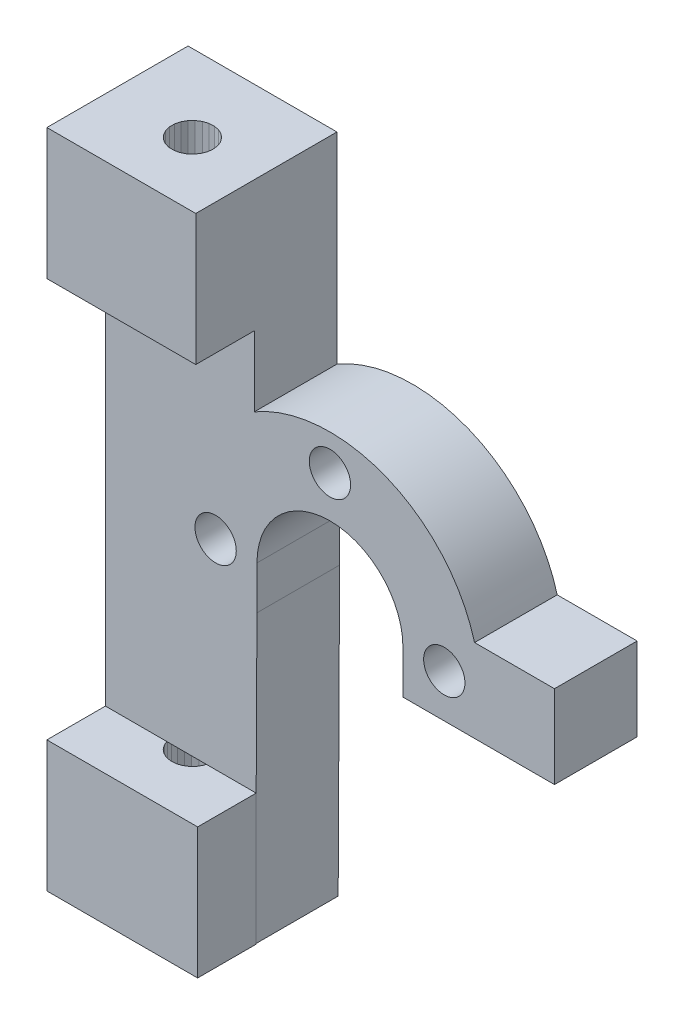
SolidWorks part; units mm, degrees
ref_plane "Front Plane" through (0, 0, 0) normal (0, 0, 1) x (1, 0, 0)
ref_plane "Top Plane" through (0, 0, 0) normal (0, 1, 0) x (1, 0, 0)
ref_plane "Right Plane" through (0, 0, 0) normal (1, 0, 0) x (0, 0, -1)
sketch "Sketch1" plane through (0, 0, 84.4516) normal (0, 0, 1) x (1, 0, 0)
  line L0 (24.9234, 11.702) -> (44.5234, 11.702) construction
  line L4 (45.6141, 11.702) -> (44.5234, 11.702) construction
  line L5 (40.0234, 11.702) -> (40.0234, 8.5665)
  line L6 (29.4234, 11.702) -> (29.4234, 8.5665)
  line L7 (40.0234, 8.5665) -> (47.0234, 8.5665)
  line L9 (45.6141, 11.702) -> (45.6141, 25.0304) construction
  line L11 (18.4234, 14.5957) -> (18.4234, 8.5665)
  line L14 (47.0234, 8.5665) -> (51.0234, 8.5665)
  line L15 (51.0234, 8.5665) -> (51.0234, 14.5957)
  line L16 (51.0234, 14.5957) -> (45.2226, 14.5957)
  line L18 (19.3206, -12.2967) -> (29.3206, -12.2967) construction
  line L20 (29.3206, 35.7033) -> (19.3206, 35.7033) construction
  line L21 (29.2311, 35.7033) -> (19.3206, 35.7033) construction
  line L22 (18.4234, 14.5957) -> (18.4234, 35.7033)
  line L23 (29.2311, 35.7033) -> (29.2311, 21.1063)
  line L25 (19.3206, -12.2967) -> (29.3206, -12.2967) construction
  line L26 (18.4234, 8.5665) -> (18.4234, -12.2967)
  line L27 (29.4234, 8.5665) -> (29.3206, -12.2967)
  line L28 (29.3206, -12.2967) -> (18.4234, -12.2967)
  line L29 (18.4234, 35.7033) -> (29.2311, 35.7033)
  circle A0 centre (43.0234, 11.702) radius 1.5 construction
  circle A1 centre (26.4234, 11.702) radius 1.5 construction
  circle A2 centre (43.0234, 11.702) radius 1.5
  circle A3 centre (26.4234, 11.702) radius 1.5
  arc A6 (40.0234, 11.702) -> (29.4234, 11.702) centre (34.7234, 11.702) ccw
  arc A7 (45.2226, 14.5957) -> (29.2311, 21.1063) centre (34.7234, 11.702) ccw
  circle A8 centre (34.7234, 20.002) radius 1.5 construction
  circle A9 centre (34.7234, 20.002) radius 1.5
  arc A12 (46.5136, 8.5665) -> (46.5753, 14.5957) centre (34.7234, 11.702) ccw construction
  dimension "D1" = 8
  dimension "D2" = 8
  dimension "D3" = 4
  dimension "D4" = 3
  dimension "D5" = 3
extrude "Boss-Extrude1" add sketch "Sketch1" along normal blind 6
sketch "Sketch2" plane through (0, 0, 90.4516) normal (0, 0, 1) x (1, 0, 0)
  line L0 (29.2311, 21.1063) -> (29.2311, 35.7033) construction
  line L1 (18.4234, 35.7033) -> (29.2311, 35.7033)
  line L2 (18.4234, 35.7033) -> (18.4234, 26.2033)
  line L3 (18.4234, 26.2033) -> (29.2311, 26.2033)
  line L4 (29.2311, 35.7033) -> (29.2311, 26.2033)
  line L6 (29.3206, -12.2967) -> (29.4234, 8.5665) construction
  line L7 (18.4234, -12.2967) -> (29.3674, -12.2967)
  line L8 (18.4234, -12.2967) -> (18.4234, -2.7967)
  line L9 (18.4234, -2.7967) -> (29.3674, -2.7967)
  line L10 (29.3674, -12.2967) -> (29.3674, -2.7967)
  dimension "D1" = 9.5
  dimension "D2" = 9.5
extrude "Boss-Extrude2" add sketch "Sketch2" along normal blind 4.25
sketch "Sketch3" plane through (0, 35.7033, 0) normal (0, 1, 0) x (1, 0, 0)
  line L0 (24.0395, -91.5074) -> (24.4148, -91.531) construction
  line L1 (23.6819, -91.3912) -> (24.0395, -91.5074) construction
  line L2 (23.3645, -91.1898) -> (23.6819, -91.3912) construction
  line L3 (23.1071, -90.9157) -> (23.3645, -91.1898) construction
  line L4 (22.926, -90.5862) -> (23.1071, -90.9157) construction
  line L5 (22.8324, -90.222) -> (22.926, -90.5862) construction
  line L6 (22.8324, -89.846) -> (22.8324, -90.222) construction
  line L7 (22.926, -89.4818) -> (22.8324, -89.846) construction
  line L8 (23.1071, -89.1523) -> (22.926, -89.4818) construction
  line L9 (23.3645, -88.8782) -> (23.1071, -89.1523) construction
  line L10 (23.6819, -88.6768) -> (23.3645, -88.8782) construction
  line L11 (24.0395, -88.5606) -> (23.6819, -88.6768) construction
  line L12 (24.4148, -88.537) -> (24.0395, -88.5606) construction
  line L13 (24.7841, -88.6074) -> (24.4148, -88.537) construction
  line L14 (25.1244, -88.7675) -> (24.7841, -88.6074) construction
  line L15 (25.4141, -89.0072) -> (25.1244, -88.7675) construction
  line L16 (25.6351, -89.3114) -> (25.4141, -89.0072) construction
  line L17 (24.4148, -91.531) -> (24.7841, -91.4606) construction
  line L18 (24.7841, -91.4606) -> (25.1244, -91.3005) construction
  line L19 (25.1244, -91.3005) -> (25.4141, -91.0608) construction
  line L20 (25.4141, -91.0608) -> (25.6351, -90.7566) construction
  line L21 (25.6351, -90.7566) -> (25.7735, -90.407) construction
  line L22 (25.7735, -90.407) -> (25.8206, -90.034) construction
  line L23 (25.8206, -90.034) -> (25.7735, -89.661) construction
  line L24 (25.7735, -89.661) -> (25.6351, -89.3114) construction
  line L25 (24.0395, -91.5074) -> (24.4148, -91.531)
  line L26 (23.6819, -91.3912) -> (24.0395, -91.5074)
  line L27 (23.3645, -91.1898) -> (23.6819, -91.3912)
  line L28 (23.1071, -90.9157) -> (23.3645, -91.1898)
  line L29 (22.926, -90.5862) -> (23.1071, -90.9157)
  line L30 (22.8324, -90.222) -> (22.926, -90.5862)
  line L31 (22.8324, -89.846) -> (22.8324, -90.222)
  line L32 (22.926, -89.4818) -> (22.8324, -89.846)
  line L33 (23.1071, -89.1523) -> (22.926, -89.4818)
  line L34 (23.3645, -88.8782) -> (23.1071, -89.1523)
  line L35 (23.6819, -88.6768) -> (23.3645, -88.8782)
  line L36 (24.0395, -88.5606) -> (23.6819, -88.6768)
  line L37 (24.4148, -88.537) -> (24.0395, -88.5606)
  line L38 (24.7841, -88.6074) -> (24.4148, -88.537)
  line L39 (25.1244, -88.7675) -> (24.7841, -88.6074)
  line L40 (25.4141, -89.0072) -> (25.1244, -88.7675)
  line L41 (25.6351, -89.3114) -> (25.4141, -89.0072)
  line L42 (24.4148, -91.531) -> (24.7841, -91.4606)
  line L43 (24.7841, -91.4606) -> (25.1244, -91.3005)
  line L44 (25.1244, -91.3005) -> (25.4141, -91.0608)
  line L45 (25.4141, -91.0608) -> (25.6351, -90.7566)
  line L46 (25.6351, -90.7566) -> (25.7735, -90.407)
  line L47 (25.7735, -90.407) -> (25.8206, -90.034)
  line L48 (25.8206, -90.034) -> (25.7735, -89.661)
  line L49 (25.7735, -89.661) -> (25.6351, -89.3114)
extrude "Cut-Extrude1" cut sketch "Sketch3" against normal up to surface (9.5 mm away) up to face at (23.8273, 26.2033, 92.5766)
sketch "Sketch4" plane through (0, -12.2967, 0) normal (0, -1, 0) x (1, 0, 0)
  line L0 (25.2768, 88.8782) -> (24.9593, 88.6768) construction
  line L1 (24.9593, 88.6768) -> (24.6017, 88.5606) construction
  line L2 (24.6017, 88.5606) -> (24.2264, 88.537) construction
  line L3 (24.2264, 88.537) -> (23.8571, 88.6074) construction
  line L4 (23.8571, 88.6074) -> (23.5169, 88.7675) construction
  line L5 (23.5169, 88.7675) -> (23.2272, 89.0072) construction
  line L6 (23.2272, 89.0072) -> (23.0062, 89.3114) construction
  line L7 (23.0062, 89.3114) -> (22.8677, 89.661) construction
  line L8 (22.8677, 89.661) -> (22.8206, 90.034) construction
  line L9 (22.8206, 90.034) -> (22.8677, 90.407) construction
  line L10 (22.8677, 90.407) -> (23.0062, 90.7566) construction
  line L11 (23.0062, 90.7566) -> (23.2272, 91.0608) construction
  line L12 (23.2272, 91.0608) -> (23.5169, 91.3005) construction
  line L13 (23.5169, 91.3005) -> (23.8571, 91.4606) construction
  line L14 (23.8571, 91.4606) -> (24.2264, 91.531) construction
  line L15 (24.2264, 91.531) -> (24.6017, 91.5074) construction
  line L16 (24.6017, 91.5074) -> (24.9593, 91.3912) construction
  line L17 (24.9593, 91.3912) -> (25.2768, 91.1898) construction
  line L18 (25.2768, 91.1898) -> (25.5341, 90.9157) construction
  line L19 (25.5341, 90.9157) -> (25.7153, 90.5862) construction
  line L20 (25.7153, 90.5862) -> (25.8088, 90.222) construction
  line L21 (25.8088, 90.222) -> (25.8088, 89.846) construction
  line L22 (25.8088, 89.846) -> (25.7153, 89.4818) construction
  line L23 (25.5341, 89.1523) -> (25.2768, 88.8782) construction
  line L24 (25.7153, 89.4818) -> (25.5341, 89.1523) construction
  line L25 (25.2768, 88.8782) -> (24.9593, 88.6768)
  line L26 (24.9593, 88.6768) -> (24.6017, 88.5606)
  line L27 (24.6017, 88.5606) -> (24.2264, 88.537)
  line L28 (24.2264, 88.537) -> (23.8571, 88.6074)
  line L29 (23.8571, 88.6074) -> (23.5169, 88.7675)
  line L30 (23.5169, 88.7675) -> (23.2272, 89.0072)
  line L31 (23.2272, 89.0072) -> (23.0062, 89.3114)
  line L32 (23.0062, 89.3114) -> (22.8677, 89.661)
  line L33 (22.8677, 89.661) -> (22.8206, 90.034)
  line L34 (22.8206, 90.034) -> (22.8677, 90.407)
  line L35 (22.8677, 90.407) -> (23.0062, 90.7566)
  line L36 (23.0062, 90.7566) -> (23.2272, 91.0608)
  line L37 (23.2272, 91.0608) -> (23.5169, 91.3005)
  line L38 (23.5169, 91.3005) -> (23.8571, 91.4606)
  line L39 (23.8571, 91.4606) -> (24.2264, 91.531)
  line L40 (24.2264, 91.531) -> (24.6017, 91.5074)
  line L41 (24.6017, 91.5074) -> (24.9593, 91.3912)
  line L42 (24.9593, 91.3912) -> (25.2768, 91.1898)
  line L43 (25.2768, 91.1898) -> (25.5341, 90.9157)
  line L44 (25.5341, 90.9157) -> (25.7153, 90.5862)
  line L45 (25.7153, 90.5862) -> (25.8088, 90.222)
  line L46 (25.8088, 90.222) -> (25.8088, 89.846)
  line L47 (25.8088, 89.846) -> (25.7153, 89.4818)
  line L48 (25.5341, 89.1523) -> (25.2768, 88.8782)
  line L49 (25.7153, 89.4818) -> (25.5341, 89.1523)
extrude "Cut-Extrude2" cut sketch "Sketch4" against normal up to surface (9.5 mm away) up to face at (23.8954, -2.7967, 92.5766)
